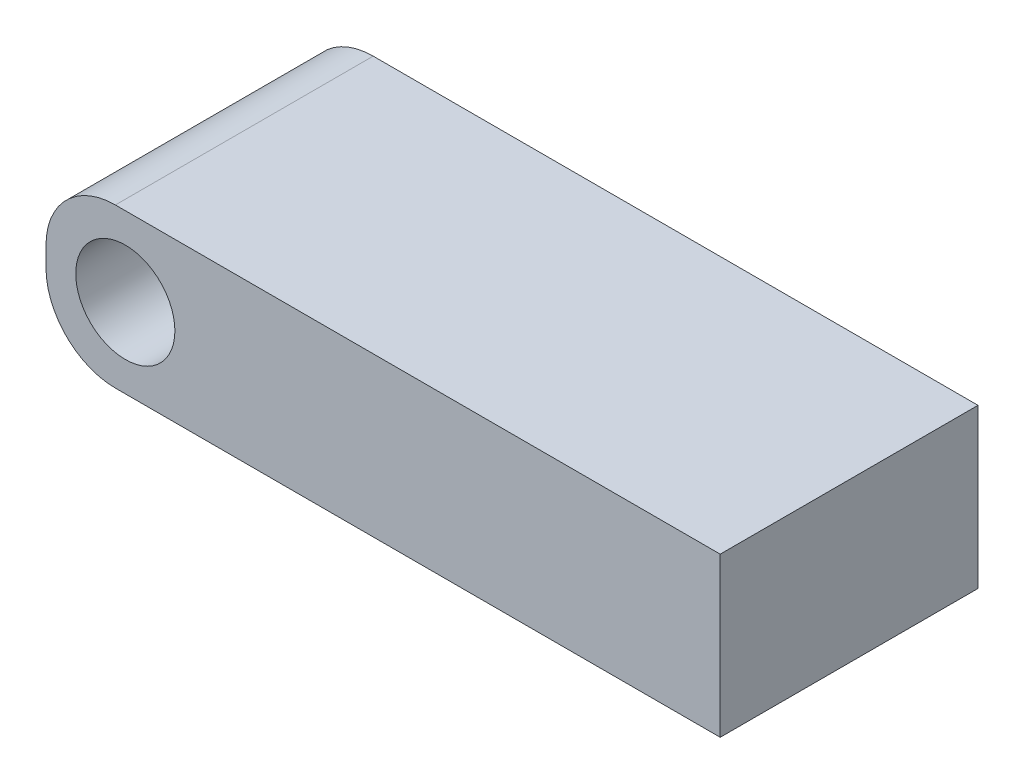
SolidWorks part; units mm, degrees
ref_plane "Front Plane" through (0, 0, 0) normal (0, 0, 1) x (1, 0, 0)
ref_plane "Top Plane" through (0, 0, 0) normal (0, 1, 0) x (1, 0, 0)
ref_plane "Right Plane" through (0, 0, 0) normal (1, 0, 0) x (0, 0, -1)
sketch "Sketch1" plane through (0, 0, 0) normal (0, 0, 1) x (1, 0, 0)
  line L0 (-23, 35) -> (-23, 10) construction
  line L1 (-19.5, 34.4286) -> (11, 34.4286)
  line L2 (-23, 30.9286) -> (-23, 29.9286)
  line L3 (-19.5, 26.4286) -> (11, 26.4286)
  line L4 (11, 34.4286) -> (11, 26.4286)
  circle A0 centre (-19, 30.4286) radius 2.5
  arc A1 (-23, 29.9286) -> (-19.5, 26.4286) centre (-19.5, 29.9286) ccw
  arc A2 (-23, 30.9286) -> (-19.5, 34.4286) centre (-19.5, 30.9286) cw
  dimension "D1" = 5
  dimension "D4" = 3.5
  dimension "D2" = 4
  dimension "D3" = 4
  dimension "D5" = 30
extrude "Boss-Extrude1" add sketch "Sketch1" along normal mid plane 13 contours L1 L4 L3 A1 L2 A2 | A0
